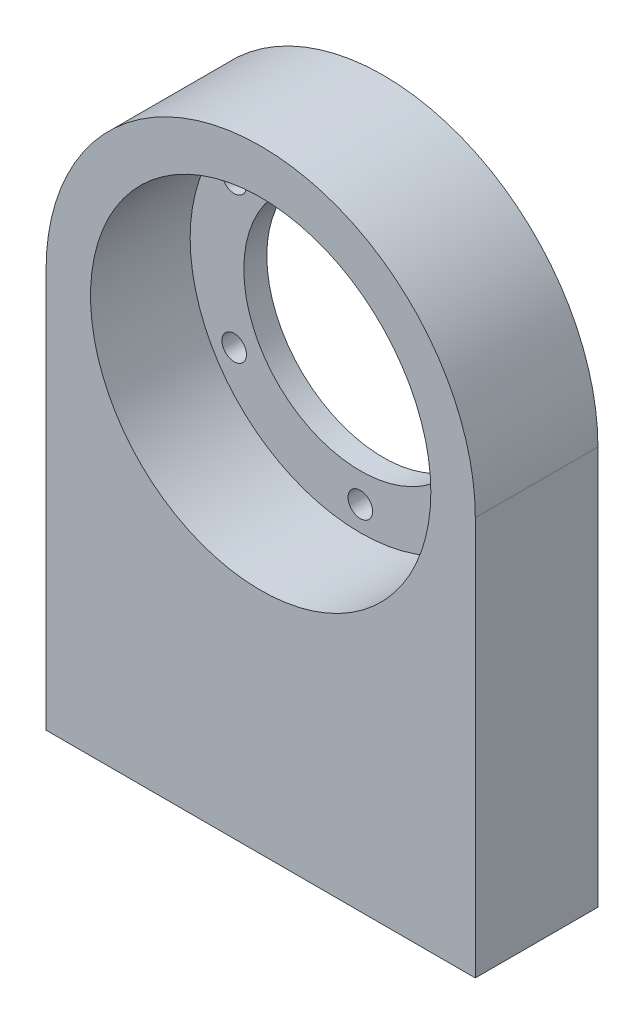
SolidWorks part; units mm, degrees
ref_plane "Plan de face" through (0, 0, 0) normal (0, 0, 1) x (1, 0, 0)
ref_plane "Plan de dessus" through (0, 0, 0) normal (0, 1, 0) x (1, 0, 0)
ref_plane "Plan de droite" through (0, 0, 0) normal (1, 0, 0) x (0, 0, -1)
sketch "Esquisse1" plane through (0, 0, 0) normal (0, 0, 1) x (1, 0, 0)
  line L1 (-14, 0) -> (14, 0) construction
  line L2 (-14, 0) -> (-14, -26)
  line L3 (-14, -26) -> (14, -26)
  line L4 (14, 0) -> (14, -26)
  circle A0 centre (0, 0) radius 14 construction
  arc A1 (-14, 0) -> (14, 0) centre (0, 0) cw
  circle A2 centre (0, 0) radius 7.6
  dimension "D1" = 28
  dimension "D3" = 15.2
  dimension "D2" = 26
extrude "Boss.-Extru.1" add sketch "Esquisse1" along normal blind 8
sketch "Esquisse2" plane through (0, 0, 8) normal (0, 0, 1) x (1, 0, 0)
  circle A0 centre (0, 0) radius 11.1
  dimension "D1" = 22.2
extrude "Enlèv. mat.-Extru.1" cut sketch "Esquisse2" against normal offset from surface (6.5 mm away) 1.5 up to face at (0, -9.5, 0)
sketch "Esquisse3" plane through (0, 0, 0) normal (0, 0, -1) x (-1, 0, 0)
  line L0 (0, 9.5) -> (0, 0) construction
  circle A0 centre (0, 9.5) radius 0.8
  circle A1 centre (8.2272, 4.75) radius 0.8
  circle A2 centre (8.2272, -4.75) radius 0.8
  circle A3 centre (0, -9.5) radius 0.8
  circle A4 centre (-8.2272, -4.75) radius 0.8
  circle A5 centre (-8.2272, 4.75) radius 0.8
  point P2 (0, 0)
  point P17 (0, 0)
  dimension "D1" = 1.6
  dimension "D2" = 9.5
  dimension "D3" = 6
extrude "Enlèv. mat.-Extru.2" cut sketch "Esquisse3" against normal up to next
sketch "Esquisse4" plane through (0, -26, 0) normal (0, -1, 0) x (1, 0, 0)
  line L0 (0, 0) -> (0, 8) construction
  line L1 (-14, 0) -> (14, 0) construction
  line L2 (-14, 8) -> (14, 8) construction
  line L3 (-10, 4) -> (10, 4) construction
  line L4 (-14, 8) -> (-14, 0) construction
  circle A0 centre (-10, 4) radius 1.5
  circle A1 centre (10, 4) radius 1.5
  point P9 (0, 4)
  dimension "D2" = 3
  dimension "D1" = 4
extrude "Enlèv. mat.-Extru.3" cut sketch "Esquisse4" against normal blind 15
